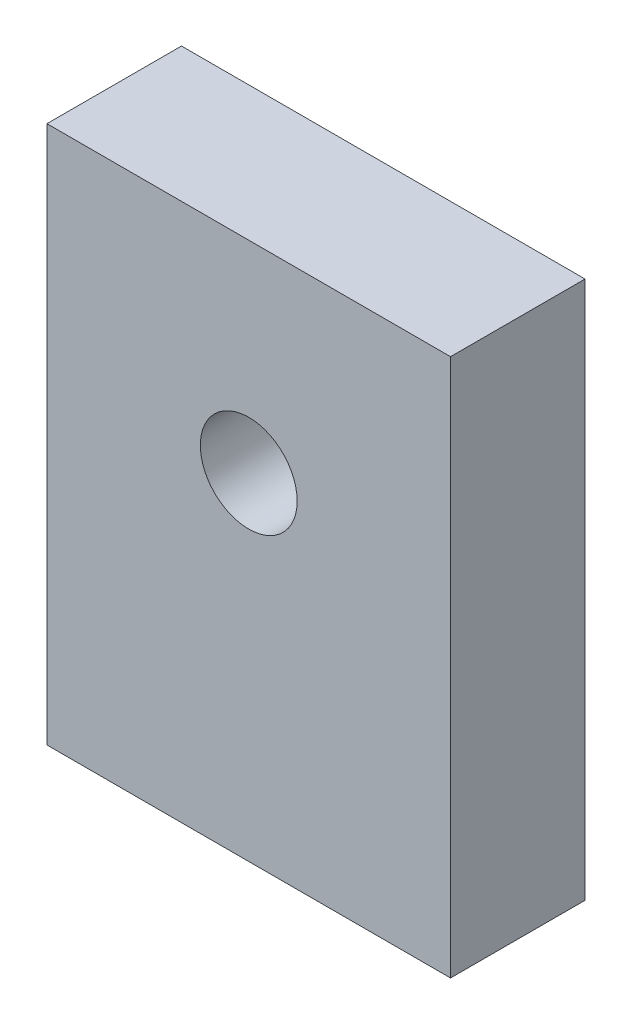
SolidWorks part; units mm, degrees
ref_plane "Front Plane" through (0, 0, 0) normal (0, 0, 1) x (1, 0, 0)
ref_plane "Top Plane" through (0, 0, 0) normal (0, 1, 0) x (1, 0, 0)
ref_plane "Right Plane" through (0, 0, 0) normal (1, 0, 0) x (0, 0, -1)
sketch "Sketch1" plane through (0, 0, 0) normal (0, 0, 1) x (1, 0, 0)
  line L0 (0, 5.0839) -> (0, 0) construction
  line L1 (-9.525, -10.7911) -> (9.525, -10.7911)
  line L2 (-9.525, -10.7911) -> (-9.525, 14.6089)
  line L3 (-9.525, 14.6089) -> (9.525, 14.6089)
  line L4 (9.525, -10.7911) -> (9.525, 14.6089)
  line L5 (0, 5.0839) -> (9.525, 5.0839) construction
  circle A0 centre (0, 5.0839) radius 2.286
  point P0 (0, 0)
  dimension "D3" = 9.525
  dimension "D4" = 4.572
  dimension "D1" = 19.05
  dimension "D2" = 25.4
extrude "Boss-Extrude1" add sketch "Sketch1" along normal blind 6.35
